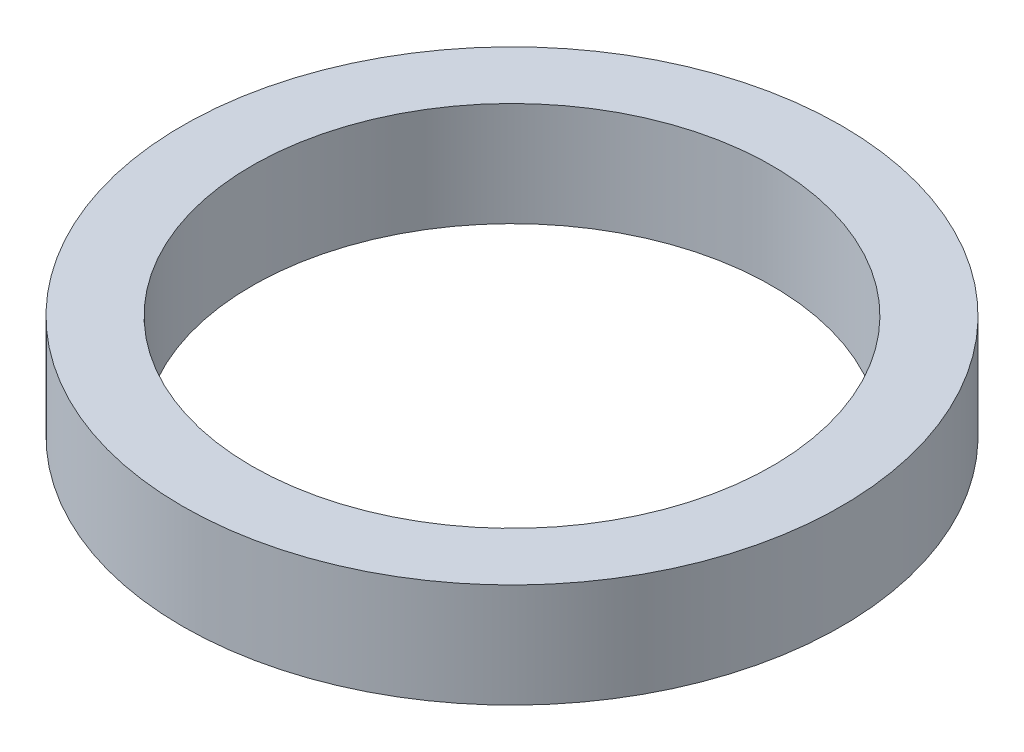
SolidWorks part; units mm, degrees
material "HYPALON"
ref_plane "Plan de face" through (0, 0, 0) normal (0, 0, 1) x (1, 0, 0)
ref_plane "Plan de dessus" through (0, 0, 0) normal (0, 1, 0) x (1, 0, 0)
ref_plane "Plan de droite" through (0, 0, 0) normal (1, 0, 0) x (0, 0, -1)
sketch "Esquisse1" plane through (0, 0, 0) normal (0, 1, 0) x (1, 0, 0)
  circle A0 centre (0, 0) radius 15
  circle A1 centre (0, 0) radius 19
  dimension "D1" = 4
extrude "Boss.-Extru.1" add sketch "Esquisse1" along normal blind 6
